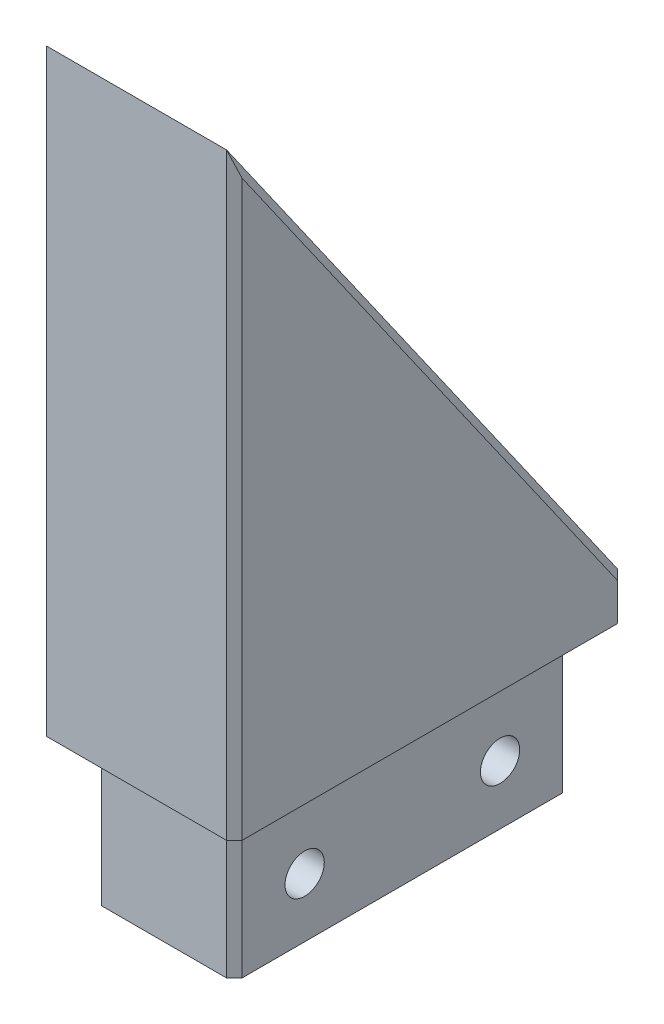
SolidWorks part; units mm, degrees
material "Nylon 101"
ref_plane "Front Plane" through (0, 0, 0) normal (0, 0, 1) x (1, 0, 0)
ref_plane "Top Plane" through (0, 0, 0) normal (0, 1, 0) x (1, 0, 0)
ref_plane "Right Plane" through (0, 0, 0) normal (1, 0, 0) x (0, 0, -1)
sketch "Sketch1" plane through (0, 0, 0) normal (1, 0, 0) x (0, 0, -1)
  line L0 (0, 0) -> (0, 77.724)
  line L1 (0, 77.724) -> (50.8, 5.1741)
  line L2 (50.8, 5.1741) -> (50.8, 0)
  line L3 (50.8, 0) -> (0, 0)
  dimension "D1" = 55
  dimension "D2" = 77.724
  dimension "D3" = 50.8
extrude "Boss-Extrude1" add sketch "Sketch1" along normal mid plane 25.4
sketch "Sketch2" plane through (0, 0, 0) normal (0, -1, 0) x (1, 0, 0)
  line L0 (0, -47.244) -> (0, -50.8) construction
  line L1 (9.144, -3.556) -> (-9.144, -3.556)
  line L2 (9.144, -3.556) -> (9.144, -47.244)
  line L3 (9.144, -47.244) -> (-9.144, -47.244)
  line L4 (-9.144, -3.556) -> (-9.144, -47.244)
  line L5 (12.7, -50.8) -> (-12.7, -50.8) construction
  line L6 (9.144, -25.4) -> (12.7, -25.4) construction
  line L7 (12.7, 0) -> (12.7, -50.8) construction
  dimension "D1" = 43.688
  dimension "D2" = 18.288
  dimension "D3" = 3.556
extrude "Boss-Extrude2" add sketch "Sketch2" along normal blind 19.05
sketch "Sketch3" plane through (9.144, 0, 0) normal (1, 0, 0) x (0, 0, -1)
  line L0 (3.556, -11.3754) -> (47.244, -11.3754) construction
  line L4 (3.556, -19.05) -> (3.556, 0) construction
  line L5 (47.244, -19.05) -> (47.244, 0) construction
  circle A1 centre (38.1, -11.3754) radius 2.5527
  circle A2 centre (12.7, -11.3754) radius 2.5527
  circle A5 centre (12.7, -11.3754) radius 2.4892 construction
  point P6 (12.7, -11.3754)
  point P7 (0, 0)
  point P14 (11.9047, -13.205)
  dimension "D2" = 9.144
  dimension "D4" = 5.1054
  dimension "D1" = 25.4
extrude "Cut-Extrude1" cut sketch "Sketch3" against normal through all
chamfer "Chamfer1" distance 1 angle 45 11 edges at (-9.144, -9.525, -3.556) (9.144, -9.525, -3.556) (-9.144, -9.525, -47.244) (9.144, -9.525, -47.244) (0, 77.724, 0) (-12.7, 2.587, -50.8) (-12.7, 41.449, -25.4) (-12.7, 38.862, 0) (12.7, 2.587, -50.8) (12.7, 41.449, -25.4) (12.7, 38.862, 0)
